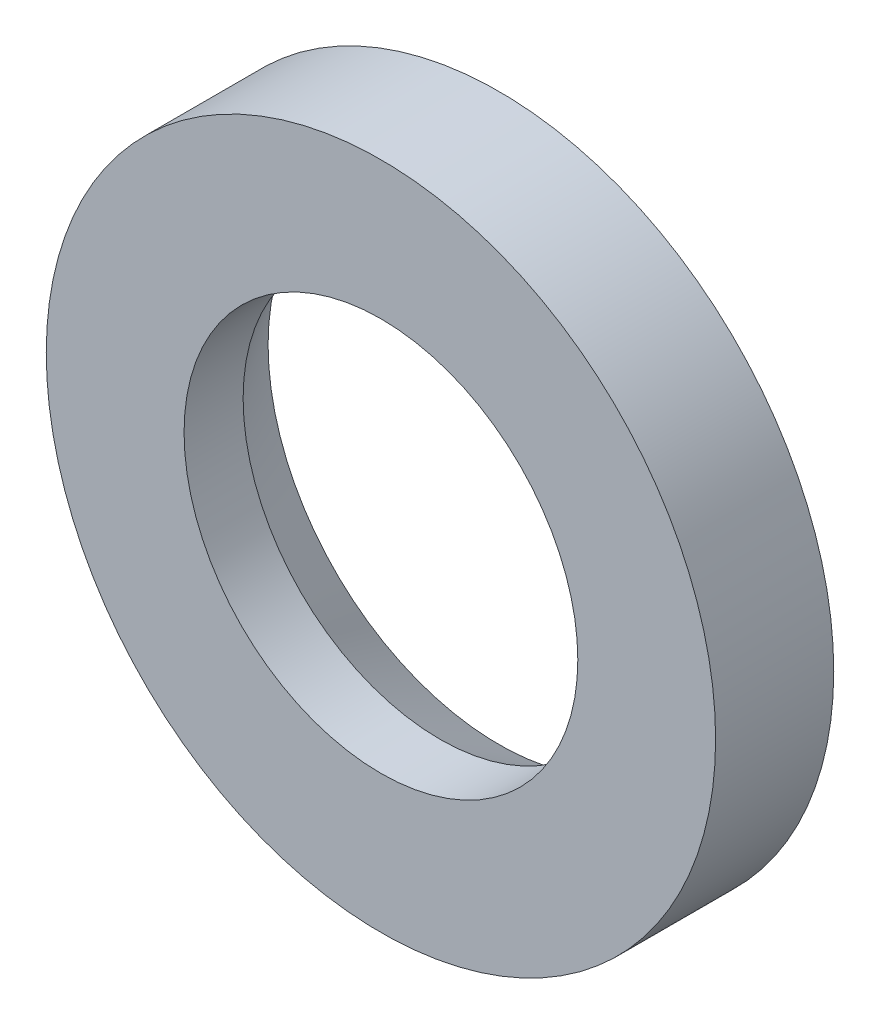
SolidWorks part; units mm, degrees
ref_plane "Front Plane" through (0, 0, 0) normal (0, 0, 1) x (1, 0, 0)
ref_plane "Top Plane" through (0, 0, 0) normal (0, 1, 0) x (1, 0, 0)
ref_plane "Right Plane" through (0, 0, 0) normal (1, 0, 0) x (0, 0, -1)
sketch "Sketch1" plane through (0, 0, 0) normal (0, 0, 1) x (1, 0, 0)
  circle A0 centre (0, 0) radius 1.7
  dimension "D1" = 3.4
extrude "Boss-Extrude1" add sketch "Sketch1" against normal blind 0.6
sketch "Sketch2" plane through (0, 0, 0) normal (0, 0, 1) x (1, 0, 0)
  circle A0 centre (0, 0) radius 1
  dimension "D1" = 2
extrude "Cut-Extrude1" cut sketch "Sketch2" against normal through all
chamfer "Chamfer1" distance 0.3 angle 30 1 edges at (1, 0, -0.6)
